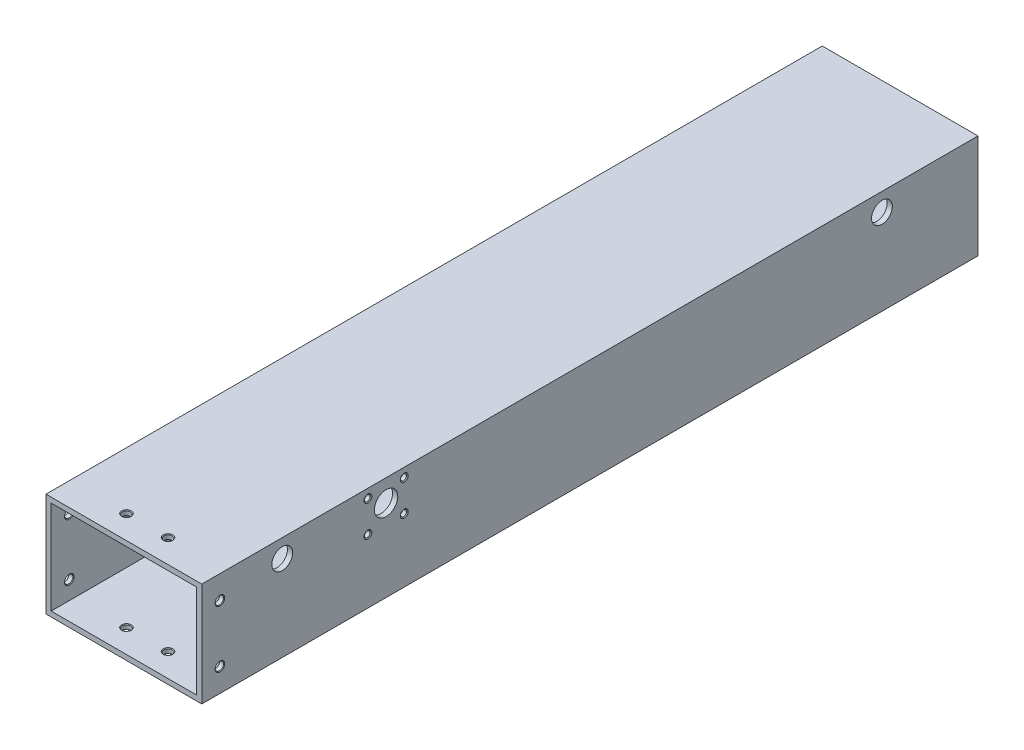
SolidWorks part; units mm, degrees
material "6063-T1"
ref_plane "Спереди" through (0, 0, 0) normal (0, 0, 1) x (1, 0, 0)
ref_plane "Сверху" through (0, 0, 0) normal (0, 1, 0) x (1, 0, 0)
ref_plane "Справа" through (0, 0, 0) normal (1, 0, 0) x (0, 0, -1)
sketch "Эскиз1" plane through (0, 0, 0) normal (0, 0, 1) x (1, 0, 0)
  line L1 (-30, 20) -> (30, 20)
  line L2 (-30, 20) -> (-30, -20)
  line L3 (-30, -20) -> (30, -20)
  line L4 (30, 20) -> (30, -20)
  line L5 (-28, 18) -> (28, 18)
  line L6 (-28, 18) -> (-28, -18)
  line L7 (-28, -18) -> (28, -18)
  line L8 (28, 18) -> (28, -18)
  dimension "D1" = 30
  dimension "D2" = 60
  dimension "D3" = 20
  dimension "D4" = 40
  dimension "D5" = 2
  dimension "D6" = 2
  dimension "D7" = 2
  dimension "D8" = 2
extrude "Вытянуть1" add sketch "Эскиз1" along normal blind 299 contours L4 L1 L2 L3 L5 L8 L7 L6
hole_wizard "Отверстие с зазором M31" positions "Эскиз3" profile "Эскиз2" hole size "M3" standard "DIN" end condition up to next
sketch "Эскиз3" plane through (-30, 0, 0) normal (-1, 0, 0) x (0, 0, 1)
  line L1 (299, 20) -> (0, 20) construction
  line L2 (299, -20) -> (0, -20) construction
  line L3 (299, 20) -> (299, -20) construction
  point P0 (292, 11)
  point P1 (292, -11)
  dimension "D1" = 7
  dimension "D2" = 9
  dimension "D4" = 9
sketch "Эскиз2" plane through (-30, 11, 292) normal (0, 1, 0) x (0, 0, 1)
  line L0 (0, 0) -> (0, 2)
  line L1 (0, 2) -> (1.85, 2)
  line L2 (1.6, 1.75) -> (1.6, 0.25)
  line L3 (1.6, 0.25) -> (1.85, 0)
  line L5 (1.85, 0) -> (0, 0)
  line L6 (-1.6, 0.25) -> (-1.85, 0) construction
  line L7 (1.85, 2) -> (1.6, 1.75)
  line L8 (-1.85, 2) -> (-1.6, 1.75) construction
  line L11 (0, -6.35) -> (0, 107.95) construction
  dimension "Диаметр сквозного отверстия" = 3.2
  dimension "Глубина сквозного отверстия" = 2
  dimension "Диаметр передней зенковки" = 3.7
  dimension "Угол передней зенковки" = 90
  dimension "Диаметр задней зенковки" = 3.7
  dimension "Угол задней зенковки" = 90
hole_wizard "Отверстие с зазором M32" positions "Эскиз5" profile "Эскиз4" hole size "M3" standard "DIN" end condition up to next
sketch "Эскиз5" plane through (30, 0, 0) normal (1, 0, 0) x (0, 0, -1)
  circle A7 centre (-292, -11) radius 1.6 construction
  circle A11 centre (-292, 11) radius 1.6 construction
  point P0 (-292, -11)
  point P1 (-292, 11)
sketch "Эскиз4" plane through (30, -11, 292) normal (0, 1, 0) x (0, 0, -1)
  line L0 (0, 0) -> (0, 2)
  line L1 (0, 2) -> (1.85, 2)
  line L2 (1.6, 1.75) -> (1.6, 0.25)
  line L3 (1.6, 0.25) -> (1.85, 0)
  line L5 (1.85, 0) -> (0, 0)
  line L6 (-1.6, 0.25) -> (-1.85, 0) construction
  line L7 (1.85, 2) -> (1.6, 1.75)
  line L8 (-1.85, 2) -> (-1.6, 1.75) construction
  line L11 (0, -6.35) -> (0, 107.95) construction
  dimension "Диаметр сквозного отверстия" = 3.2
  dimension "Глубина сквозного отверстия" = 2
  dimension "Диаметр передней зенковки" = 3.7
  dimension "Угол передней зенковки" = 90
  dimension "Диаметр задней зенковки" = 3.7
  dimension "Угол задней зенковки" = 90
hole_wizard "Отверстие с зазором M33" positions "Эскиз7" profile "Эскиз6" hole size "M3" standard "DIN" end condition up to next
sketch "Эскиз7" plane through (0, -20, 0) normal (0, -1, 0) x (1, 0, 0)
  line L2 (-30, 299) -> (-30, 0) construction
  line L3 (-30, 299) -> (30, 299) construction
  point P0 (-8, 290)
  point P1 (8, 290)
  dimension "D1" = 9
  dimension "D2" = 16
  dimension "D4" = 22
sketch "Эскиз6" plane through (-8, -20, 290) normal (1, 0, 0) x (0, 0, -1)
  line L0 (0, 0) -> (0, 2)
  line L1 (0, 2) -> (1.85, 2)
  line L2 (1.6, 1.75) -> (1.6, 0.25)
  line L3 (1.6, 0.25) -> (1.85, 0)
  line L5 (1.85, 0) -> (0, 0)
  line L6 (-1.6, 0.25) -> (-1.85, 0) construction
  line L7 (1.85, 2) -> (1.6, 1.75)
  line L8 (-1.85, 2) -> (-1.6, 1.75) construction
  line L11 (0, -6.35) -> (0, 107.95) construction
  dimension "Диаметр сквозного отверстия" = 3.2
  dimension "Глубина сквозного отверстия" = 2
  dimension "Диаметр передней зенковки" = 3.7
  dimension "Угол передней зенковки" = 90
  dimension "Диаметр задней зенковки" = 3.7
  dimension "Угол задней зенковки" = 90
hole_wizard "Отверстие с зазором M34" positions "Эскиз9" profile "Эскиз8" hole size "M3" standard "DIN" end condition up to next
sketch "Эскиз9" plane through (0, 20, 0) normal (0, 1, 0) x (-1, 0, 0)
  circle A0 centre (-8, 290) radius 1.6 construction
  circle A1 centre (8, 290) radius 1.6 construction
  point P0 (-8, 290)
  point P1 (8, 290)
sketch "Эскиз8" plane through (8, 20, 290) normal (1, 0, 0) x (0, 0, 1)
  line L0 (0, 0) -> (0, 2)
  line L1 (0, 2) -> (1.85, 2)
  line L2 (1.6, 1.75) -> (1.6, 0.25)
  line L3 (1.6, 0.25) -> (1.85, 0)
  line L5 (1.85, 0) -> (0, 0)
  line L6 (-1.6, 0.25) -> (-1.85, 0) construction
  line L7 (1.85, 2) -> (1.6, 1.75)
  line L8 (-1.85, 2) -> (-1.6, 1.75) construction
  line L11 (0, -6.35) -> (0, 107.95) construction
  dimension "Диаметр сквозного отверстия" = 3.2
  dimension "Глубина сквозного отверстия" = 2
  dimension "Диаметр передней зенковки" = 3.7
  dimension "Угол передней зенковки" = 90
  dimension "Диаметр задней зенковки" = 3.7
  dimension "Угол задней зенковки" = 90
sketch "Эскиз12" plane through (0, -20, 0) normal (0, 1, 0) x (1, 0, 0)
  line L0 (-30, 0) -> (30, 0) construction
  line L1 (30, -299) -> (30, 0) construction
  circle A0 centre (12, -35) radius 4
  circle A1 centre (19, -240.5) radius 4
  dimension "D1" = 8
  dimension "D2" = 205.5
  dimension "D3" = 35
  dimension "D4" = 11
  dimension "D6" = 18
extrude "Воздух вход-выход" cut sketch "Эскиз12" along normal up to next contours A1 | A0
sketch "Эскиз13" [suppressed] plane through (0, -20, 0) normal (0, -1, 0) x (1, 0, 0)
  circle A0 centre (19, 240.5) radius 8
  circle M7 centre (19, 240.5) radius 4.5
  dimension "D1" = 16
extrude "Вырез-Вытянуть2" [suppressed] cut sketch "Эскиз13" against normal blind 0.5 contours A0 M7
hole_wizard "Зенковка для винта с потайной головкой M31" [suppressed] positions "Трехмерный эскиз1" profile "Эскиз14" countersink size "M3" standard "DIN"
sketch3d "Трехмерный эскиз1"
  point P0 (24, 18, 10.5)
  point P2 (24, 18, 22.5)
  point P4 (28, 14, 10.5)
  point P6 (28, 14, 22.5)
  point P8 (28, -14, 10.5)
  point P10 (28, -14, 22.5)
  point P12 (24, -18, 10.5)
  point P14 (24, -18, 22.5)
  point P16 (-24, -18, 10.5)
  point P18 (-24, -18, 22.5)
  point P20 (-24, 18, 10.5)
  point P22 (-24, 18, 22.5)
  point P24 (-28, 14, 10.5)
  point P26 (-28, 14, 22.5)
  point P28 (-28, -14, 10.5)
  point P30 (-28, -14, 22.5)
  dimension "D1" = 10.5
  dimension "D2" = 12
  dimension "D3" = 4
  dimension "D4" = 4
  dimension "D5" = 10.5
  dimension "D6" = 4
  dimension "D7" = 12
  dimension "D8" = 4
  dimension "D9" = 12
sketch "Эскиз14" plane through (24, 18, 10.5) normal (1, 0, 0) x (0, 0, -1)
  line L0 (0, 0) -> (0, 2)
  line L1 (0, 2) -> (1.725, 2)
  line L2 (1.6, 1.875) -> (1.6, 1.25)
  line L3 (1.6, 1.25) -> (2.85, 0)
  line L5 (2.85, 0) -> (0, 0)
  line L6 (-1.6, 1.25) -> (-2.85, 0) construction
  line L7 (1.725, 2) -> (1.6, 1.875)
  line L8 (-1.725, 2) -> (-1.6, 1.875) construction
  line L11 (0, -6.35) -> (0, 107.95) construction
  dimension "Диаметр сквозного отверстия" = 3.2
  dimension "Глубина сквозного отверстия" = 2
  dimension "Диаметр передней зенковки" = 5.7
  dimension "Угол передней зенковки" = 90
  dimension "Диаметр задней зенковки" = 3.45
  dimension "Угол задней зенковки" = 90
sketch "Эскиз15" plane through (30, 0, 0) normal (1, 0, 0) x (0, 0, -1)
  line L0 (-299, 18) -> (0, 18) construction
  line L2 (0, 20) -> (0, -20) construction
  circle A0 centre (-37, 13) radius 4
  circle A1 centre (-268, 13) radius 4
  circle A2 centre (-228, 11.5) radius 4.5
  dimension "D1" = 5
  dimension "D3" = 37
  dimension "D4" = 8
  dimension "D5" = 9
  dimension "D2" = 268
  dimension "D6" = 6.5
  dimension "D7" = 40
extrude "Вырез-Вытянуть3" cut sketch "Эскиз15" against normal up to next contours A0 | A1 | A2
hole_wizard "Отверстие обработанное метчиком #4-401" positions "Эскиз17" profile "Эскиз16" tap size "#4-40" standard "Ansi (в дюймах)" end condition up to next
sketch "Эскиз17" plane through (30, 0, 0) normal (1, 0, 0) x (0, 0, -1)
  circle A0 centre (-228, 11.5) radius 4.5 construction
  point P0 (-235, 16.5)
  point P1 (-235, 4.5)
  point P4 (-221, 4.5)
  point P7 (-221, 16.5)
  dimension "D2" = 5
  dimension "D1" = 14
  dimension "D3" = 7
  dimension "D4" = 12
sketch "Эскиз16" plane through (30, 16.5, 235) normal (0, 1, 0) x (0, 0, -1)
  line L0 (0, 0) -> (0, 2)
  line L1 (0, 2) -> (1.524, 2)
  line L2 (1.1303, 1.7243) -> (1.1303, 0.2757)
  line L3 (1.1303, 0.2757) -> (1.524, 0)
  line L5 (1.524, 0) -> (0, 0)
  line L6 (-1.1303, 0.2757) -> (-1.524, 0) construction
  line L7 (1.524, 2) -> (1.1303, 1.7243)
  line L8 (-1.524, 2) -> (-1.1303, 1.7243) construction
  line L11 (0, -6.35) -> (0, 107.95) construction
  dimension "Диаметр проходного сверла" = 2.2606
  dimension "Глубина проходного сверла" = 2
  dimension "Диаметр передней зенковки" = 3.048
  dimension "Угол передней зенковки" = 110
  dimension "Диаметр задней зенковки" = 3.048
  dimension "Угол задней зенковки" = 110
cosmetic thread "Отверстие резьбы1" parameters "D2"=2.8448
cosmetic thread "Отверстие резьбы2" parameters "D2"=2.8448
cosmetic thread "Отверстие резьбы3" parameters "D2"=2.8448
cosmetic thread "Отверстие резьбы4" parameters "D2"=2.8448
